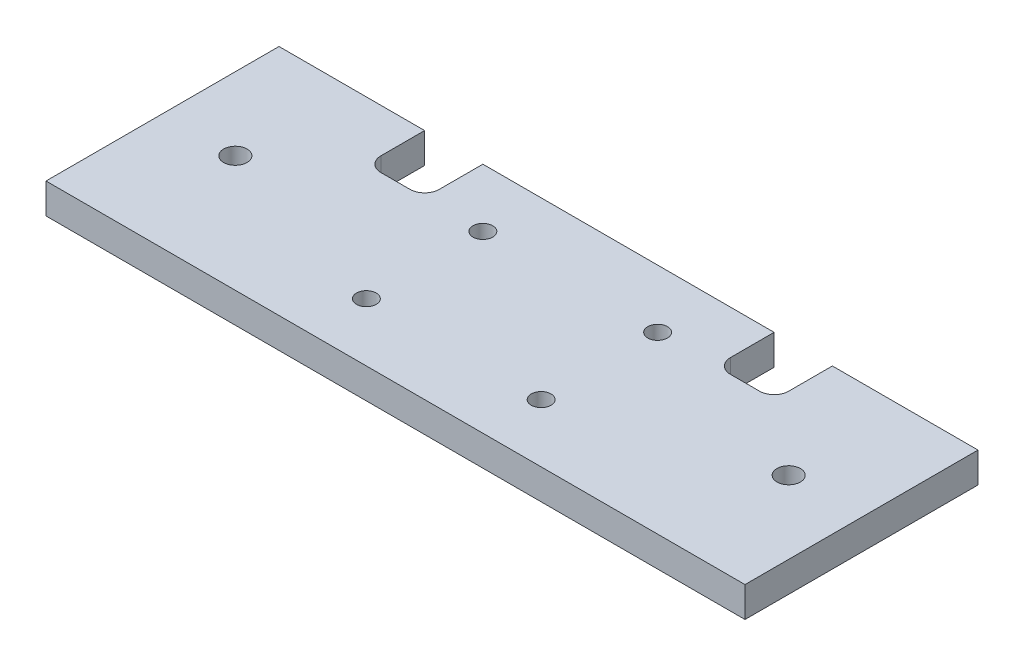
SolidWorks part; units mm, degrees
material "Acrylic (BLUE)"
ref_plane "Front Plane" through (0, 0, 0) normal (0, 0, 1) x (1, 0, 0)
ref_plane "Top Plane" through (0, 0, 0) normal (0, 1, 0) x (1, 0, 0)
ref_plane "Right Plane" through (0, 0, 0) normal (1, 0, 0) x (0, 0, -1)
sketch "Sketch1" plane through (0, 0, 0) normal (0, 1, 0) x (1, 0, 0)
  line L0 (-76.2, 25.4) -> (76.2, -25.4) construction
  line L1 (-76.2, 25.4) -> (76.2, 25.4)
  line L2 (-76.2, 25.4) -> (-76.2, -25.4)
  line L3 (-76.2, -25.4) -> (76.2, -25.4)
  line L4 (76.2, 25.4) -> (76.2, -25.4)
  dimension "D1" = 152.4
  dimension "D2" = 50.8
extrude "Boss-Extrude1" add sketch "Sketch1" along normal blind 6.604
sketch "Sketch2" plane through (0, 6.604, 0) normal (0, 1, 0) x (1, 0, 0)
  line L0 (76.2, 25.4) -> (-76.2, 25.4) construction
  line L1 (-44.45, 25.4) -> (-31.75, 25.4)
  line L2 (-44.45, 25.4) -> (-44.45, 15.875)
  line L3 (-41.275, 12.7) -> (-34.925, 12.7)
  line L4 (-31.75, 25.4) -> (-31.75, 15.875)
  arc A0 (-31.75, 15.875) -> (-34.925, 12.7) centre (-34.925, 15.875) cw
  arc A1 (-44.45, 15.875) -> (-41.275, 12.7) centre (-41.275, 15.875) ccw
  point P8 (-31.75, 12.7)
  point P11 (-44.45, 12.7)
  dimension "D4" = 3.175
  dimension "D1" = 12.7
  dimension "D2" = 12.7
  dimension "D3" = 31.75
extrude "Cut-Extrude1" cut sketch "Sketch2" against normal through all
mirror "Mirror1" about plane through (0, 0, 0) normal (1, 0, 0) of "Cut-Extrude1"
hole_wizard "1/4-20 Tapped Hole1" positions "Sketch4" profile "Sketch3" tap size "1/4-20" standard "ANSI Inch"
sketch "Sketch4" plane through (0, 6.604, 0) normal (0, 1, 0) x (1, 0, 0)
  line L0 (-60.325, 0) -> (0, 0) construction
  line L1 (0, 0) -> (60.325, 0) construction
  point P0 (-60.325, 0)
  point P2 (60.325, 0)
  dimension "D1" = 60.325
sketch "Sketch3" plane through (-60.325, 6.604, 0) normal (1, 0, 0) x (0, 0, 1)
  line L0 (0, 0) -> (0, 18.0438)
  line L1 (0, 18.0438) -> (2.5527, 16.51)
  line L2 (2.5527, 16.51) -> (2.5527, 0)
  line L5 (2.5527, 0) -> (0, 0)
  line L10 (0, 18.0438) -> (-2.5527, 16.51) construction
  line L11 (0, -6.35) -> (0, 107.95) construction
  dimension "Tap Drill Dia." = 5.1054
  dimension "Tap Drill Depth" = 16.51
  dimension "Drill Angle" = 118
hole_wizard "#8 Clearance Hole1" positions "Sketch6" profile "Sketch5" hole size "#8" standard "ANSI Inch"
sketch "Sketch6" plane through (0, 6.604, 0) normal (0, 1, 0) x (1, 0, 0)
  line L3 (-19.05, 25.4) -> (-19.05, 12.7) construction
  line L4 (31.75, 25.4) -> (-31.75, 25.4) construction
  line L5 (-19.05, 12.7) -> (-19.05, -12.7) construction
  line L6 (-19.05, -12.7) -> (-19.05, -25.4) construction
  line L7 (-76.2, -25.4) -> (76.2, -25.4) construction
  line L8 (19.05, 25.4) -> (19.05, 12.7) construction
  line L9 (19.05, 12.7) -> (19.05, -12.7) construction
  line L10 (19.05, -12.7) -> (19.05, -25.4) construction
  point P4 (-19.05, 12.7)
  point P6 (-19.05, -12.7)
  point P27 (19.05, 12.7)
  point P29 (19.05, -12.7)
  dimension "D1" = 12.7
  dimension "D2" = 19.05
  dimension "D3" = 19.05
sketch "Sketch5" plane through (-19.05, 6.604, -12.7) normal (1, 0, 0) x (0, 0, 1)
  line L0 (0, 0) -> (0, 8.9134)
  line L1 (0, 8.9134) -> (2.1526, 7.62)
  line L2 (2.1526, 7.62) -> (2.1526, 0)
  line L5 (2.1526, 0) -> (0, 0)
  line L10 (0, 8.9134) -> (-2.1527, 7.62) construction
  line L11 (0, -6.35) -> (0, 107.95) construction
  dimension "Hole Dia." = 4.3053
  dimension "Hole Depth" = 7.62
  dimension "Drill Angle" = 118
other "Move Face1" [suppressed] parameters "D1"=0.0508
